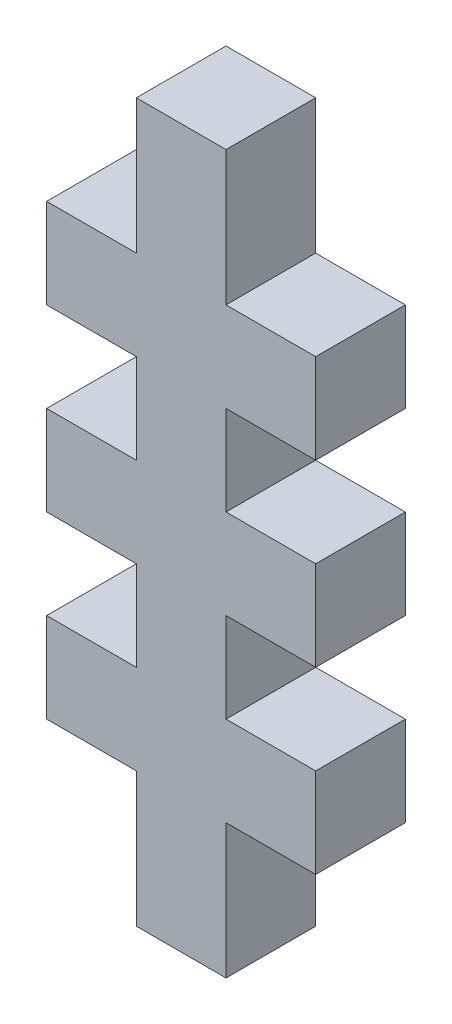
SolidWorks part; units mm, degrees
ref_plane "Plan de face" through (0, 0, 0) normal (0, 0, 1) x (1, 0, 0)
ref_plane "Plan de dessus" through (0, 0, 0) normal (0, 1, 0) x (1, 0, 0)
ref_plane "Plan de droite" through (0, 0, 0) normal (1, 0, 0) x (0, 0, -1)
sketch "Esquisse6" plane through (0, 0, 0) normal (0, 0, 1) x (1, 0, 0)
  line L1 (-7.5, 20) -> (7.5, 20)
  line L2 (-7.5, 20) -> (-7.5, -20)
  line L3 (-7.5, -20) -> (7.5, -20)
  line L4 (7.5, 20) -> (7.5, -20)
  dimension "D1" = 40
  dimension "D2" = 15
  dimension "D3" = 7.5
  dimension "D4" = 20
extrude "Boss.-Extru.3" add sketch "Esquisse6" along normal blind 5
sketch "Esquisse7" plane through (0, 0, 0) normal (0, 0, 1) x (1, 0, 0)
  line L0 (-7.5, 20) -> (-7.5, -20) construction
  line L1 (-7.5, 20) -> (-2.5, 20)
  line L2 (-7.5, 20) -> (-7.5, 12.5)
  line L3 (-7.5, 12.5) -> (-2.5, 12.5)
  line L4 (-2.5, 20) -> (-2.5, 12.5)
  line L5 (7.5, 20) -> (-7.5, 20) construction
  dimension "D1" = 5
  dimension "D2" = 7.5
  dimension "D3" = 0
  dimension "D4" = 0
extrude "Enlèv. mat.-Extru.4" cut sketch "Esquisse7" along normal blind 5
mirror "Symétrie3" about plane through (0, 0, 0) normal (0, 1, 0) of "Enlèv. mat.-Extru.4"
mirror "Symétrie4" about plane through (0, 0, 0) normal (1, 0, 0) of "Symétrie3", "Enlèv. mat.-Extru.4"
sketch "Esquisse9" plane through (0, 0, 5) normal (0, 0, 1) x (1, 0, 0)
  line L0 (-7.5, 12.5) -> (-7.5, -12.5) construction
  line L1 (-7.5, 7.5) -> (-2.5, 7.5)
  line L2 (-7.5, 7.5) -> (-7.5, 2.5)
  line L3 (-7.5, 2.5) -> (-2.5, 2.5)
  line L4 (-2.5, 7.5) -> (-2.5, 2.5)
  line L5 (-7.5, 12.5) -> (-2.5, 12.5) construction
  dimension "D1" = 5
  dimension "D2" = 5
  dimension "D3" = 5
extrude "Enlèv. mat.-Extru.6" cut sketch "Esquisse9" against normal blind 5
mirror "Symétrie5" about plane through (0, 0, 0) normal (0, 1, 0) of "Enlèv. mat.-Extru.6"
mirror "Symétrie6" about plane through (0, 0, 0) normal (1, 0, 0) of "Symétrie5", "Enlèv. mat.-Extru.6"
